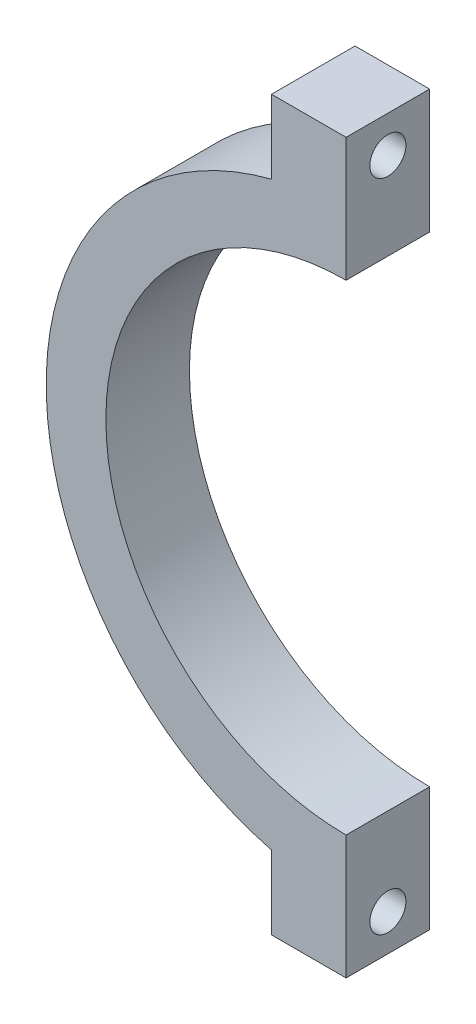
SolidWorks part; units mm, degrees
ref_plane "Front Plane" through (0, 0, 0) normal (0, 0, 1) x (1, 0, 0)
ref_plane "Top Plane" through (0, 0, 0) normal (0, 1, 0) x (1, 0, 0)
ref_plane "Right Plane" through (0, 0, 0) normal (1, 0, 0) x (0, 0, -1)
sketch "Sketch1" plane through (0, 0, 0) normal (0, 0, 1) x (1, 0, 0)
  line L0 (0, -80.5) -> (0, -122)
  line L1 (0, -122) -> (-25, -122)
  line L2 (-25, -122) -> (-25, -97.3409)
  line L3 (0, 80.5) -> (0, 122)
  line L4 (0, 122) -> (-25, 122)
  line L5 (-25, 122) -> (-25, 97.3409)
  arc A0 (0, 80.5) -> (0, -80.5) centre (0, 0) ccw
  arc A1 (-25, 97.3409) -> (-25, -97.3409) centre (0, 0) ccw
  dimension "D1" = 100.5
  dimension "D2" = 80.5
  dimension "D3" = 122
  dimension "D4" = 25
  dimension "D5" = 25
  dimension "D6" = 122
extrude "Boss-Extrude1" add sketch "Sketch1" along normal blind 28
sketch "Sketch2" plane through (0, 0, 0) normal (1, 0, 0) x (0, 0, -1)
  line L0 (-28, 80.5) -> (-28, 122) construction
  line L1 (-28, -122) -> (-28, -80.5) construction
  line L2 (-28, -122) -> (0, -122) construction
  line L3 (-28, 122) -> (0, 122) construction
  circle A0 centre (-14, 109.75) radius 6.05
  circle A1 centre (-14, -109.75) radius 6.05
  dimension "D1" = 12.1
  dimension "D3" = 12.1
  dimension "D2" = 14
  dimension "D4" = 14
  dimension "D5" = 12.25
  dimension "D6" = 12.25
extrude "Cut-Extrude1" cut sketch "Sketch2" against normal blind 28
